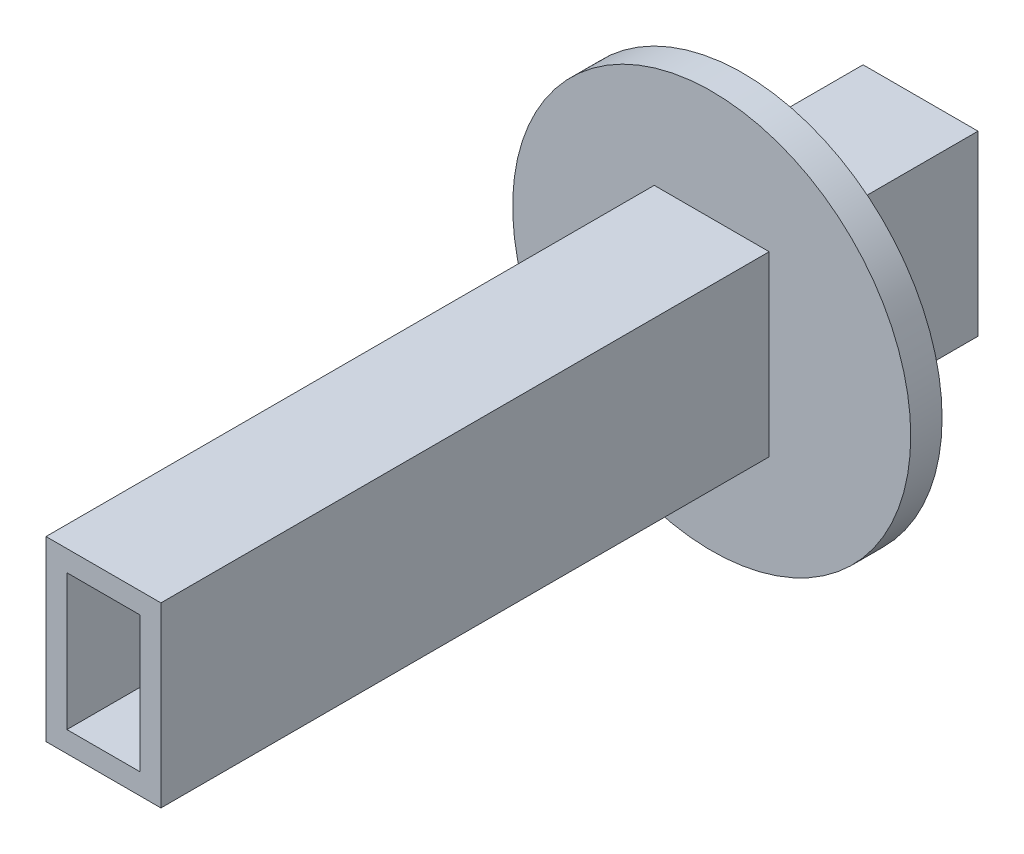
SolidWorks part; units mm, degrees
ref_plane "Front Plane" through (0, 0, 0) normal (0, 0, 1) x (1, 0, 0)
ref_plane "Top Plane" through (0, 0, 0) normal (0, 1, 0) x (1, 0, 0)
ref_plane "Right Plane" through (0, 0, 0) normal (1, 0, 0) x (0, 0, -1)
sketch "Sketch1" plane through (0, 0, 0) normal (0, 0, 1) x (1, 0, 0)
  line L1 (0, 0) -> (7, 0)
  line L2 (0, 0) -> (0, 13)
  line L3 (0, 13) -> (7, 13)
  line L4 (7, 0) -> (7, 13)
  line L5 (-2, -2) -> (9, -2)
  line L6 (-2, -2) -> (-2, 15)
  line L7 (-2, 15) -> (9, 15)
  line L8 (9, -2) -> (9, 15)
  dimension "D1" = 7
  dimension "D2" = 13
  dimension "D3" = 2
  dimension "D4" = 2
  dimension "D5" = 2
  dimension "D6" = 2
extrude "Boss-Extrude1" add sketch "Sketch1" along normal blind 76.2
sketch "Sketch2" plane through (0, 0, 0) normal (0, 0, -1) x (-1, 0, 0)
  line L1 (-9, -2) -> (2, -2)
  line L2 (-9, -2) -> (-9, 15)
  line L3 (-9, 15) -> (2, 15)
  line L4 (2, -2) -> (2, 15)
extrude "Boss-Extrude2" add sketch "Sketch2" along normal blind 2
sketch "Sketch3" plane through (0, -2, 0) normal (0, -1, 0) x (-1, 0, 0)
  line L0 (-9, 2) -> (2, 2) construction
  line L1 (-7, 0) -> (0, 0)
  line L2 (-7, 0) -> (-7, -11)
  line L3 (-7, -11) -> (0, -11)
  line L4 (0, 0) -> (0, -11)
  line L5 (2, -76.2) -> (2, 2) construction
  line L6 (-9, -76.2) -> (-9, 2) construction
  dimension "D1" = 2
  dimension "D2" = 2
  dimension "D3" = 2
  dimension "D4" = 11
extrude "Cut-Extrude1" cut sketch "Sketch3" against normal up to surface (2 mm away) up to face at (3.5, 0, 38.1)
ref_plane "Plane1" through (0, 0, 14.986) normal (0, 0, 1) x (1, 0, 0)
sketch "Sketch4" plane through (0, 0, 14.986) normal (0, 0, 1) x (1, 0, 0)
  line L0 (0, 13) -> (0, 0) construction
  line L2 (-2, 15) -> (9, 15)
  line L3 (-2, 15) -> (-2, -2)
  line L4 (-2, -2) -> (9, -2)
  line L5 (9, 15) -> (9, -2)
  circle A0 centre (3.5, 6.5) radius 19.05
  point P11 (0, 0)
  point P12 (0, 0)
  point P13 (0, 0)
  dimension "D3" = 38.1
  dimension "D1" = 6.5
  dimension "D2" = 3.5
extrude "Boss-Extrude3" add sketch "Sketch4" along normal blind 3
sketch "Sketch5" plane through (0, 0, 14.986) normal (0, 0, -1) x (-1, 0, 0)
  line L1 (-9, 15) -> (2, 15)
  line L2 (-9, 15) -> (-9, -2)
  line L3 (-9, -2) -> (2, -2)
  line L4 (2, 15) -> (2, -2)
  circle A0 centre (-3.5, 6.5) radius 12.7
  dimension "D1" = 25.4
extrude "Boss-Extrude4" add sketch "Sketch5" along normal blind 2.54
